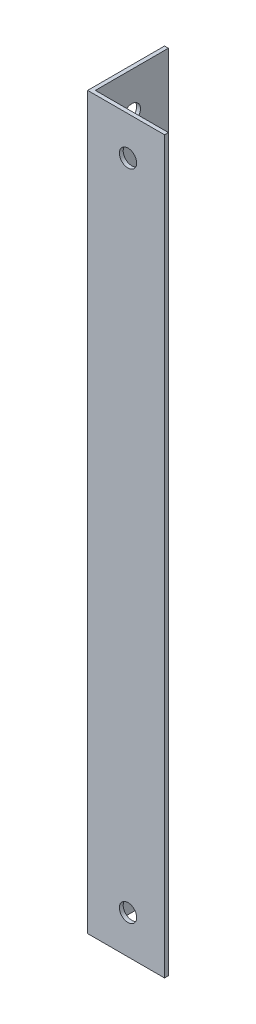
SolidWorks part; units mm, degrees
material "1060 Сплав"
ref_plane "Спереди" through (0, 0, 0) normal (0, 0, 1) x (1, 0, 0)
ref_plane "Сверху" through (0, 0, 0) normal (0, 1, 0) x (1, 0, 0)
ref_plane "Справа" through (0, 0, 0) normal (1, 0, 0) x (0, 0, -1)
sketch "Эскиз1" plane through (0, 0, 0) normal (0, 1, 0) x (1, 0, 0)
  line L0 (0, 0) -> (0, 20)
  line L1 (0, 20) -> (1, 20)
  line L2 (1, 20) -> (1, 1)
  line L3 (1, 1) -> (20, 1)
  line L4 (20, 1) -> (20, 0)
  line L5 (20, 0) -> (0, 0)
  dimension "D1" = 1
  dimension "D2" = 20
extrude "Бобышка-Вытянуть1" add sketch "Эскиз1" along normal blind 190
sketch "Эскиз2" plane through (1, 0, 0) normal (1, 0, 0) x (0, 0, -1)
  line L0 (10.5, 190) -> (10.5, 0) construction
  line L1 (1, 190) -> (20, 190) construction
  line L2 (1, 0) -> (20, 0) construction
  circle A0 centre (10.5, 10) radius 2.25
  circle A1 centre (10.5, 180) radius 2.25
  dimension "D1" = 10
  dimension "D2" = 4.5
  dimension "D3" = 10
  dimension "D4" = 4.5
extrude "Вырез-Вытянуть1" cut sketch "Эскиз2" against normal through all
sketch "Эскиз3" plane through (0, 0, -1) normal (0, 0, -1) x (-1, 0, 0)
  line L0 (-10.5, 190) -> (-10.5, 0) construction
  line L1 (-20, 190) -> (-1, 190) construction
  line L2 (-20, 0) -> (-1, 0) construction
  circle A0 centre (-10.5, 180) radius 2.25
  circle A1 centre (-10.5, 10) radius 2.25
  dimension "D1" = 4.5
  dimension "D3" = 10
  dimension "D4" = 4.5
  dimension "D2" = 10
extrude "Вырез-Вытянуть2" cut sketch "Эскиз3" against normal through all
